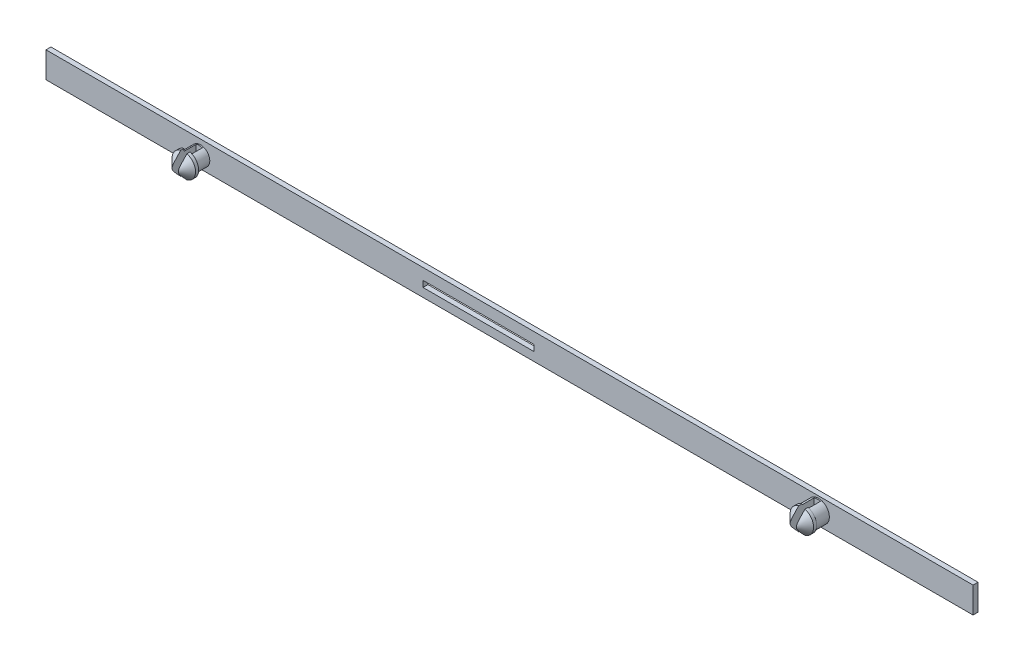
SolidWorks part; units mm, degrees
ref_plane "Přední rovina" through (0, 0, 0) normal (0, 0, 1) x (1, 0, 0)
ref_plane "Horní rovina" through (0, 0, 0) normal (0, 1, 0) x (1, 0, 0)
ref_plane "Pravá rovina" through (0, 0, 0) normal (1, 0, 0) x (0, 0, -1)
sketch "Skica2" plane through (0, 0, 0) normal (0, 0, 1) x (1, 0, 0)
  line L1 (-75, 2.1) -> (75, 2.1)
  line L2 (-75, 2.1) -> (-75, -2.1)
  line L3 (-75, -2.1) -> (75, -2.1)
  line L4 (75, 2.1) -> (75, -2.1)
  line L5 (-75, 2.1) -> (75, -2.1) construction
  line L6 (-75, -2.1) -> (75, 2.1) construction
  line L7 (4, 0.3) -> (-14, 0.3)
  line L8 (4, 0.3) -> (4, -0.7)
  line L9 (4, -0.7) -> (-14, -0.7)
  line L10 (-14, 0.3) -> (-14, -0.7)
  line L11 (4, 0.3) -> (-14, -0.7) construction
  line L12 (4, -0.7) -> (-14, 0.3) construction
  point P0 (0, 0)
  point P5 (-5, -0.2)
  dimension "D1" = 4.2
  dimension "D2" = 150
  dimension "D3" = 1
  dimension "D4" = 18
  dimension "D5" = 61
extrude "Přidat vysunutím2" add sketch "Skica2" along normal blind 0.8
sketch "Skica3" plane through (0, 0, 0.8) normal (0, 0, 1) x (1, 0, 0)
  line L0 (-75, 2.1) -> (-75, -2.1) construction
  line L1 (75, -2.1) -> (75, 2.1) construction
  line L2 (75, 2.1) -> (-75, 2.1) construction
  line L3 (-75, -2.1) -> (75, -2.1) construction
  circle A0 centre (-50, -0.2) radius 1.5
  circle A1 centre (50, 0) radius 1.75
  dimension "D1" = 3
  dimension "D3" = 3.5
  dimension "D2" = 25
  dimension "D4" = 25
  dimension "D5" = 2.3
  dimension "D6" = 1.9
extrude "Přidat vysunutím3" add sketch "Skica3" along normal blind 2.2
sketch "Skica5" plane through (0, 0, 3) normal (0, 0, 1) x (1, 0, 0)
  circle A0 centre (-50, -0.2) radius 1.9
  circle A1 centre (50, 0) radius 1.9
  dimension "D1" = 3.8
  dimension "D2" = 3.8
extrude "Přidat vysunutím5" add sketch "Skica5" along normal blind 2
chamfer "Zkosení2" distance 1.5 angle 45 2 edges at (51.9, 0, 5) (-48.1, -0.2, 5)
sketch "Skica7" plane through (0, 0, 5) normal (0, 0, 1) x (1, 0, 0)
  line L1 (-49.5, 2.3) -> (-50.5, 2.3)
  line L2 (-49.5, 2.3) -> (-49.5, -2.7)
  line L3 (-49.5, -2.7) -> (-50.5, -2.7)
  line L4 (-50.5, 2.3) -> (-50.5, -2.7)
  line L5 (-49.5, 2.3) -> (-50.5, -2.7) construction
  line L6 (-49.5, -2.7) -> (-50.5, 2.3) construction
  line L7 (49.5, 2.5) -> (50.5, 2.5)
  line L8 (49.5, 2.5) -> (49.5, -2.5)
  line L9 (49.5, -2.5) -> (50.5, -2.5)
  line L10 (50.5, 2.5) -> (50.5, -2.5)
  line L11 (49.5, 2.5) -> (50.5, -2.5) construction
  line L12 (49.5, -2.5) -> (50.5, 2.5) construction
  point P0 (-50, -0.2)
  point P5 (50, 0)
  dimension "D1" = 5
  dimension "D2" = 1
  dimension "D3" = 5
  dimension "D4" = 1
extrude "Odebrat vysunutím1" cut sketch "Skica7" against normal blind 4
equation "\"1.5.000mm\"=10"
